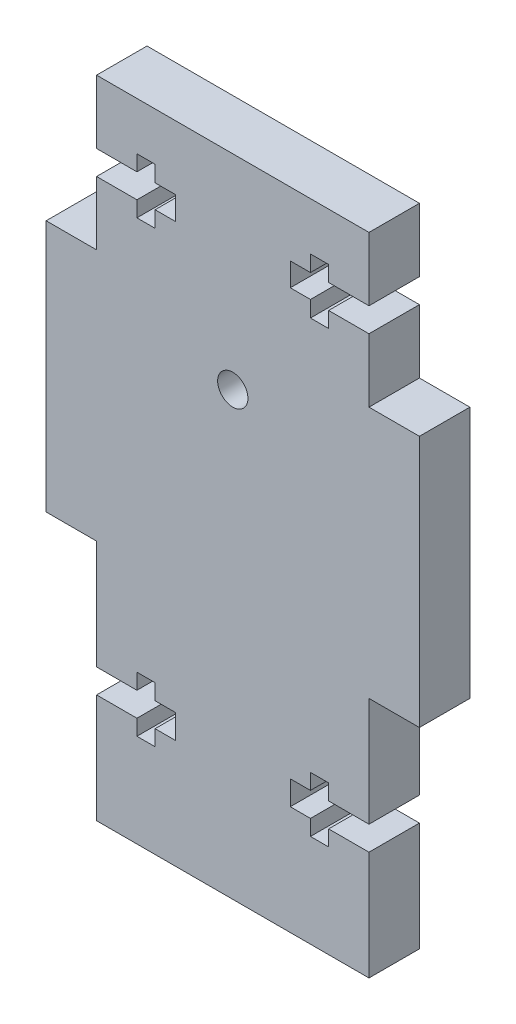
SolidWorks part; units mm, degrees
material "Acrylic (Medium-high impact)"
ref_plane "Front Plane" through (0, 0, 0) normal (0, 0, 1) x (1, 0, 0)
ref_plane "Top Plane" through (0, 0, 0) normal (0, 1, 0) x (1, 0, 0)
ref_plane "Right Plane" through (0, 0, 0) normal (1, 0, 0) x (0, 0, -1)
sketch "Sketch1" plane through (0, 0, 0) normal (0, 0, 1) x (1, 0, 0)
  line L0 (0, 0) -> (0, 64) construction
  line L1 (-13.5, 0) -> (13.5, 0)
  line L2 (13.5, 0) -> (13.5, 24)
  line L3 (13.5, 24) -> (18.5, 24)
  line L4 (18.5, 24) -> (18.5, 49)
  line L5 (18.5, 49) -> (13.5, 49)
  line L6 (13.5, 49) -> (13.5, 64)
  line L7 (13.5, 64) -> (-13.5, 64)
  line L8 (-13.5, 49) -> (-13.5, 64)
  line L9 (-18.5, 49) -> (-13.5, 49)
  line L10 (-18.5, 24) -> (-18.5, 49)
  line L11 (-13.5, 24) -> (-18.5, 24)
  line L12 (-13.5, 0) -> (-13.5, 24)
  circle A0 centre (0, 43.75) radius 1.5
  dimension "D1" = 15
  dimension "D2" = 25
  dimension "D3" = 24
  dimension "D4" = 5
  dimension "D5" = 13.5
extrude "Boss-Extrude1" add sketch "Sketch1" along normal blind 5
sketch "Sketch2" plane through (0, 0, 5) normal (0, 0, 1) x (1, 0, 0)
  line L0 (-13.5, 56.5) -> (13.5, 56.5) construction
  line L1 (-13.5, 64) -> (-13.5, 49) construction
  line L2 (13.5, 49) -> (13.5, 64) construction
  line L3 (-13.5, 56.5) -> (-13.5, 57.7)
  line L4 (-13.5, 57.7) -> (-9.5, 57.7)
  line L5 (-9.5, 57.7) -> (-9.5, 59.25)
  line L6 (-9.5, 59.25) -> (-7.7, 59.25)
  line L7 (-7.7, 59.25) -> (-7.7, 57.6542)
  line L8 (-7.7, 57.6542) -> (-5.7, 57.6542)
  line L9 (-5.7, 57.6542) -> (-5.7, 55.3458)
  line L10 (-7.7, 55.3458) -> (-5.7, 55.3458)
  line L11 (-7.7, 53.75) -> (-7.7, 55.3458)
  line L12 (-9.5, 53.75) -> (-7.7, 53.75)
  line L13 (-9.5, 55.3) -> (-9.5, 53.75)
  line L14 (-13.5, 55.3) -> (-9.5, 55.3)
  line L15 (-13.5, 56.5) -> (-13.5, 55.3)
  line L16 (0, 64) -> (0, 0) construction
  line L17 (13.5, 64) -> (-13.5, 64) construction
  line L18 (-13.5, 0) -> (13.5, 0) construction
  line L19 (13.5, 56.5) -> (13.5, 55.3)
  line L20 (13.5, 55.3) -> (9.5, 55.3)
  line L21 (9.5, 55.3) -> (9.5, 53.75)
  line L22 (9.5, 53.75) -> (7.7, 53.75)
  line L23 (7.7, 53.75) -> (7.7, 55.3458)
  line L24 (7.7, 55.3458) -> (5.7, 55.3458)
  line L25 (5.7, 57.6542) -> (5.7, 55.3458)
  line L26 (7.7, 57.6542) -> (5.7, 57.6542)
  line L27 (7.7, 59.25) -> (7.7, 57.6542)
  line L28 (9.5, 59.25) -> (7.7, 59.25)
  line L29 (9.5, 57.7) -> (9.5, 59.25)
  line L30 (13.5, 57.7) -> (9.5, 57.7)
  line L31 (13.5, 56.5) -> (13.5, 57.7)
  line L32 (-13.5, 12) -> (13.5, 12) construction
  line L33 (-13.5, 24) -> (-13.5, 0) construction
  line L34 (13.5, 0) -> (13.5, 24) construction
  line L35 (-13.5, 10.8) -> (-13.5, 13.2)
  line L36 (-13.5, 13.2) -> (-9.5, 13.2)
  line L37 (-9.5, 13.2) -> (-9.5, 14.75)
  line L38 (-9.5, 14.75) -> (-7.7, 14.75)
  line L39 (-7.7, 14.75) -> (-7.7, 13.2)
  line L40 (-7.7, 13.2) -> (-5.7, 13.2)
  line L41 (-5.7, 13.2) -> (-5.7, 10.8)
  line L42 (-7.7, 10.8) -> (-5.7, 10.8)
  line L43 (-7.7, 9.25) -> (-7.7, 10.8)
  line L44 (-9.5, 9.25) -> (-7.7, 9.25)
  line L45 (-9.5, 10.8) -> (-9.5, 9.25)
  line L46 (-13.5, 10.8) -> (-9.5, 10.8)
  line L47 (13.5, 10.8) -> (9.5, 10.8)
  line L48 (9.5, 10.8) -> (9.5, 9.25)
  line L49 (9.5, 9.25) -> (7.7, 9.25)
  line L50 (7.7, 9.25) -> (7.7, 10.8)
  line L51 (7.7, 10.8) -> (5.7, 10.8)
  line L52 (5.7, 13.2) -> (5.7, 10.8)
  line L53 (7.7, 13.2) -> (5.7, 13.2)
  line L54 (7.7, 14.75) -> (7.7, 13.2)
  line L55 (9.5, 14.75) -> (7.7, 14.75)
  line L56 (9.5, 13.2) -> (9.5, 14.75)
  line L57 (13.5, 13.2) -> (9.5, 13.2)
  line L58 (13.5, 10.8) -> (13.5, 13.2)
  point P15 (-5.7, 56.5)
  point P41 (5.7, 56.5)
  point P56 (-5.7, 12)
  point P73 (5.7, 12)
  dimension "D1" = 4
  dimension "D2" = 1.8
  dimension "D3" = 2
  dimension "D4" = 2.4
  dimension "D5" = 5.5
  dimension "D6" = 2.4
  dimension "D7" = 5.5
extrude "Cut-Extrude2" cut sketch "Sketch2" against normal through all
